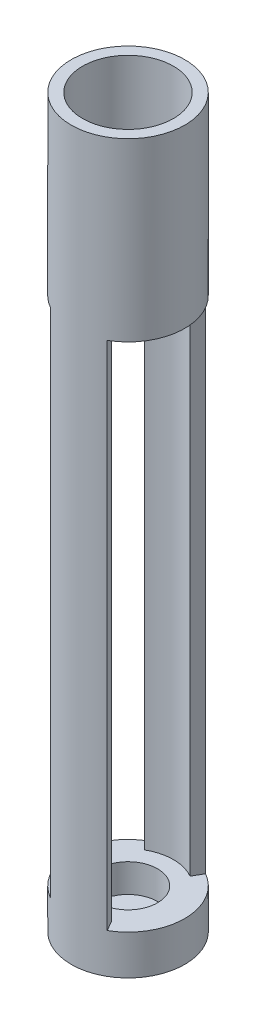
SolidWorks part; units mm, degrees
material "ABS PC"
ref_plane "Front Plane" through (0, 0, 0) normal (0, 0, 1) x (1, 0, 0)
ref_plane "Top Plane" through (0, 0, 0) normal (0, 1, 0) x (1, 0, 0)
ref_plane "Right Plane" through (0, 0, 0) normal (1, 0, 0) x (0, 0, -1)
sketch "Sketch1" plane through (0, 0, 0) normal (0, 1, 0) x (1, 0, 0)
  circle A0 centre (0, 0) radius 5
  point P5 (0, 0)
  dimension "D1" = 10
extrude "Boss-Extrude1" add sketch "Sketch1" along normal blind 3.5
sketch "Sketch2" plane through (0, 3.5, 0) normal (0, 1, 0) x (1, 0, 0)
  circle A0 centre (0, 0) radius 2.6
  dimension "D1" = 5.2
extrude "Cut-Extrude1" cut sketch "Sketch2" against normal blind 2.5
sketch "Sketch3" plane through (0, 3.5, 0) normal (0, 1, 0) x (1, 0, 0)
  line L0 (2.5, -4.3301) -> (2, -3.4641)
  line L1 (-2.5, 4.3301) -> (-2, 3.4641)
  line L2 (2.5, 4.3301) -> (2, 3.4641)
  line L3 (-2.3859, 0) -> (1.8022, 0) construction
  line L4 (-2.5, -4.3301) -> (-2, -3.4641)
  arc A2 (-2.5, 4.3301) -> (2.5, 4.3301) centre (0, 0) cw
  arc A3 (2, 3.4641) -> (-2, 3.4641) centre (0, 0) ccw
  arc A4 (2, -3.4641) -> (-2, -3.4641) centre (0, 0) cw
  arc A5 (-2.5, -4.3301) -> (2.5, -4.3301) centre (0, 0) ccw
  circle M4 centre (0, 0) radius 5
extrude "Boss-Extrude2" add sketch "Sketch3" along normal blind 45 contours L0 A4 L4 M4 | A3 L2 L1 M4
sketch "Sketch14" plane through (0, 48.5, 0) normal (0, 1, 0) x (1, 0, 0)
  circle A0 centre (0, 0) radius 5
  circle A1 centre (0, 0) radius 1.3
  dimension "D1" = 3.7
extrude "Boss-Extrude8" add sketch "Sketch14" along normal blind 3
sketch "Sketch15" plane through (0, 51.5, 0) normal (0, 1, 0) x (1, 0, 0)
  circle A0 centre (0, 0) radius 5
  circle A1 centre (0, 0) radius 2.6
  dimension "D1" = 2.4
extrude "Boss-Extrude9" add sketch "Sketch15" along normal blind 2.5
sketch "Sketch7" plane through (0, 48.5, 0) normal (0, -1, 0) x (1, 0, 0)
  line L0 (0, 0) -> (0, 2.5) construction
  circle A0 centre (0, 2.5) radius 1
extrude "Cut-Extrude2" cut sketch "Sketch7" against normal blind 2
pattern_circular "CirPattern1" count 6 over 360 about axis through (0, 0, 0) along (0, 1, 0) of "Cut-Extrude2"
sketch "Sketch12" plane through (0, 54, 0) normal (0, 1, 0) x (1, 0, 0)
  circle A0 centre (0, -3) radius 0.2
extrude "Cut-Extrude3" cut sketch "Sketch12" along direction (0, 1, 0) on the side against the normal up to next (3.5 mm away) and the other way through all
pattern_circular "CirPattern2" count 6 over 360 about axis through (0, 0, 0) along (0, 1, 0) of "Cut-Extrude3"
sketch "Sketch16" plane through (0, 54, 0) normal (0, 1, 0) x (1, 0, 0)
  circle A0 centre (0, 0) radius 5
  circle A1 centre (0, 0) radius 4
  dimension "D1" = 1
extrude "Boss-Extrude10" add sketch "Sketch16" along normal blind 10
